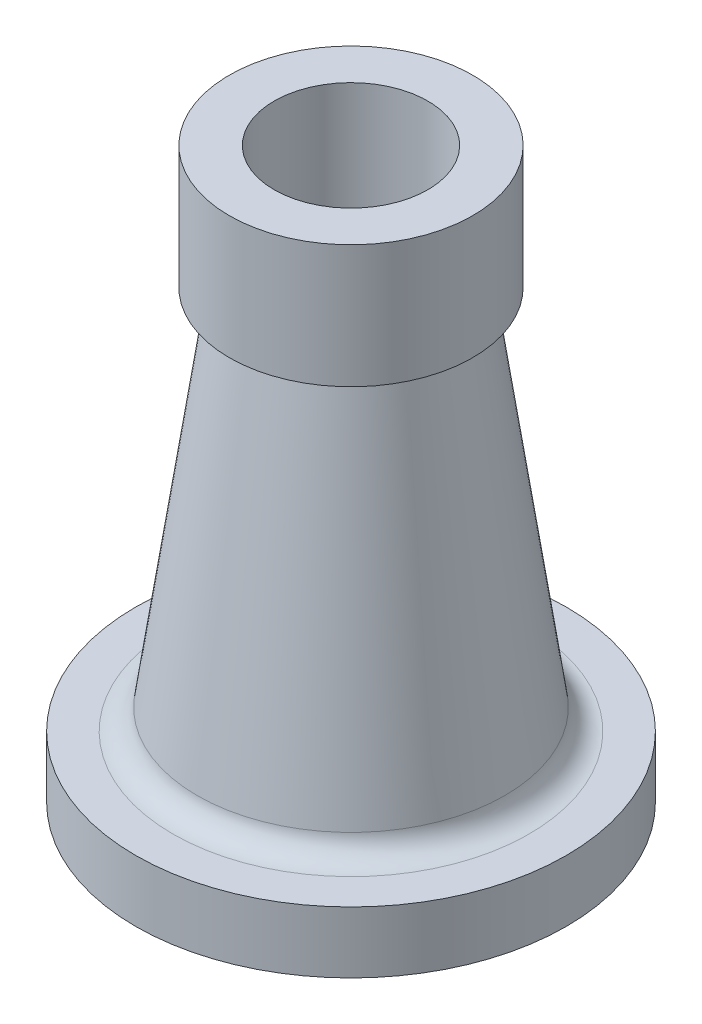
SolidWorks part; units mm, degrees
ref_plane "Front Plane" through (0, 0, 0) normal (0, 0, 1) x (1, 0, 0)
ref_plane "Top Plane" through (0, 0, 0) normal (0, 1, 0) x (1, 0, 0)
ref_plane "Right Plane" through (0, 0, 0) normal (1, 0, 0) x (0, 0, -1)
sketch "Sketch1" plane through (0, 0, 0) normal (0, 0, 1) x (1, 0, 0)
  line L0 (0, 76.1737) -> (0, -92.7527) construction
  line L1 (0, -92.7527) -> (0, -136.2578) construction
  line L2 (39.5879, 60.7213) -> (39.5879, 20.7213)
  line L3 (39.5879, 20.7213) -> (34.1542, 20.7213)
  line L4 (33.1644, 19.5789) -> (50, -97.4181)
  line L5 (57.9184, -104.2787) -> (70, -104.2787)
  line L6 (70, -104.2787) -> (70, -124.2787)
  line L7 (70, -124.2787) -> (50, -124.2787)
  line L8 (50, -124.2787) -> (50, -122.2787)
  line L9 (25, 60.7213) -> (25, 6.1068)
  line L10 (39.5879, 60.7213) -> (25, 60.7213)
  line L11 (25, 6.1068) -> (35.6976, -68.2352)
  line L12 (35.6976, -68.2352) -> (43.3305, -121.2787)
  line L13 (43.3305, -121.2787) -> (49, -121.2787)
  arc A0 (57.9184, -104.2787) -> (50, -97.4181) centre (57.9184, -96.2787) cw
  arc A1 (50, -122.2787) -> (49, -121.2787) centre (49, -122.2787) ccw
  arc A2 (33.1644, 19.5789) -> (34.1542, 20.7213) centre (34.1542, 19.7213) cw
  point P20 (50, -121.2787)
  point P23 (33, 20.7213)
  dimension "D3" = 8
  dimension "D12" = 1
  dimension "D13" = 1
  dimension "D1" = 70
  dimension "D2" = 40
  dimension "D4" = 33
  dimension "D5" = 20
  dimension "D6" = 185
  dimension "D7" = 50
  dimension "D8" = 25
  dimension "D9" = 50
  dimension "D10" = 3
  dimension "D11" = 10
revolve "Revolve1" add sketch "Sketch1" angle 360 about L0
